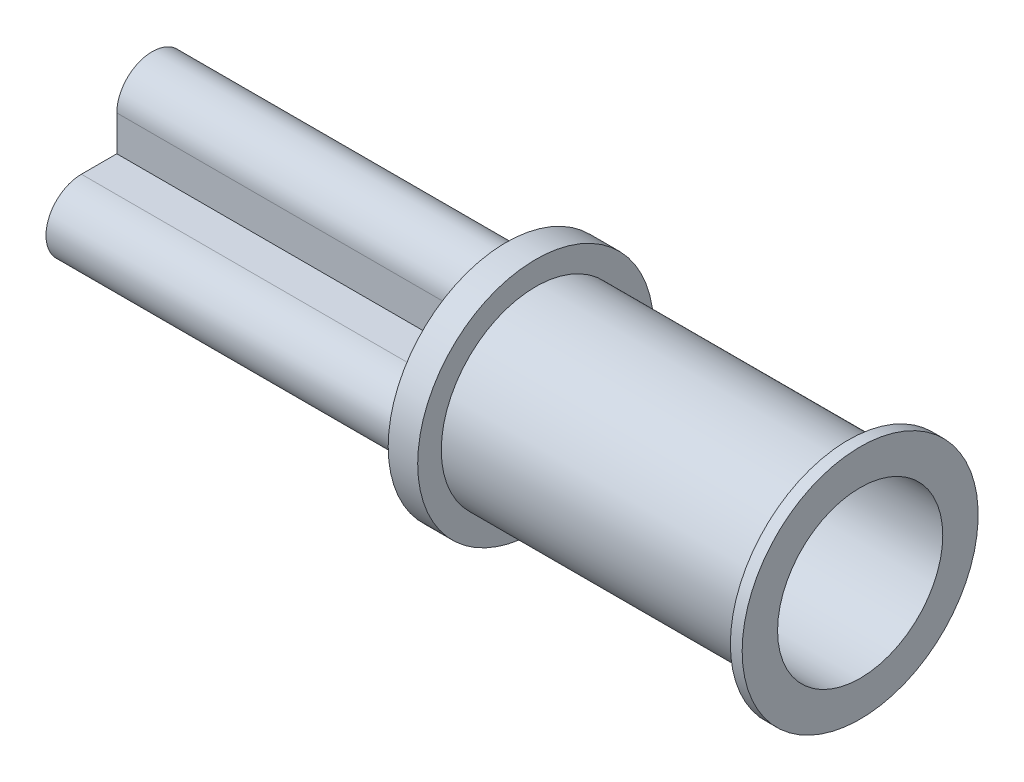
SolidWorks part; units mm, degrees
material "PVC Rigid"
ref_plane "Front Plane" through (0, 0, 0) normal (0, 0, 1) x (1, 0, 0)
ref_plane "Top Plane" through (0, 0, 0) normal (0, 1, 0) x (1, 0, 0)
ref_plane "Right Plane" through (0, 0, 0) normal (1, 0, 0) x (0, 0, -1)
sketch "Sketch1" plane through (0, 0, 0) normal (0, 0, 1) x (1, 0, 0)
  line L0 (0, 0) -> (87.134, 0) construction
  line L1 (0, 1.778) -> (0, 2.54)
  line L2 (0, 2.54) -> (0.635, 2.54)
  line L3 (0.635, 2.54) -> (0.635, 2.032)
  line L4 (0.635, 2.032) -> (7.366, 2.032)
  line L5 (0, 1.778) -> (0, 0)
  line L6 (0, 0) -> (0.635, 0)
  line L7 (0.635, 0) -> (0.635, 1.778)
  line L9 (7.366, 2.032) -> (7.366, 2.54)
  line L10 (7.366, 2.54) -> (7.62, 2.54)
  line L11 (7.62, 2.54) -> (7.62, 1.778)
  line L14 (0.635, 1.778) -> (7.62, 1.778)
  dimension "D1" = 0.254
  dimension "D2" = 0.635
  dimension "D4" = 7.62
  dimension "D5" = 0.254
  dimension "D7" = 1.778
  dimension "D8" = 2.54
revolve "Revolve1" add sketch "Sketch1" angle 360 about L0
sketch "Sketch3" plane through (0, 0, 0) normal (1, 0, 0) x (0, 0, -1)
  line L0 (-1.524, 0) -> (1.524, 0) construction
  line L1 (-1.524, 0.762) -> (-0.762, 0.762)
  line L2 (-1.524, -0.762) -> (-0.762, -0.762)
  line L3 (0, 1.524) -> (0, -1.524) construction
  line L4 (0.762, 1.524) -> (0.762, 0.762)
  line L5 (-0.762, 1.524) -> (-0.762, 0.762)
  line L6 (-0.762, -0.762) -> (-0.762, -1.524)
  line L7 (0.762, -0.762) -> (0.762, -1.524)
  line L8 (0.762, -0.762) -> (1.524, -0.762)
  line L9 (0.762, 0.762) -> (1.524, 0.762)
  arc A0 (-1.524, 0.762) -> (-1.524, -0.762) centre (-1.524, 0) ccw
  arc A1 (1.524, -0.762) -> (1.524, 0.762) centre (1.524, 0) ccw
  arc A2 (0.762, 1.524) -> (-0.762, 1.524) centre (0, 1.524) ccw
  arc A3 (-0.762, -1.524) -> (0.762, -1.524) centre (0, -1.524) ccw
  circle A4 centre (0, 0) radius 2.286 construction
  point P2 (0, 0)
  point P7 (0, 0)
  dimension "D3" = 4.572
  dimension "D1" = 1.524
  dimension "D2" = 1.524
extrude "Boss-Extrude1" add sketch "Sketch3" against normal blind 7.62
